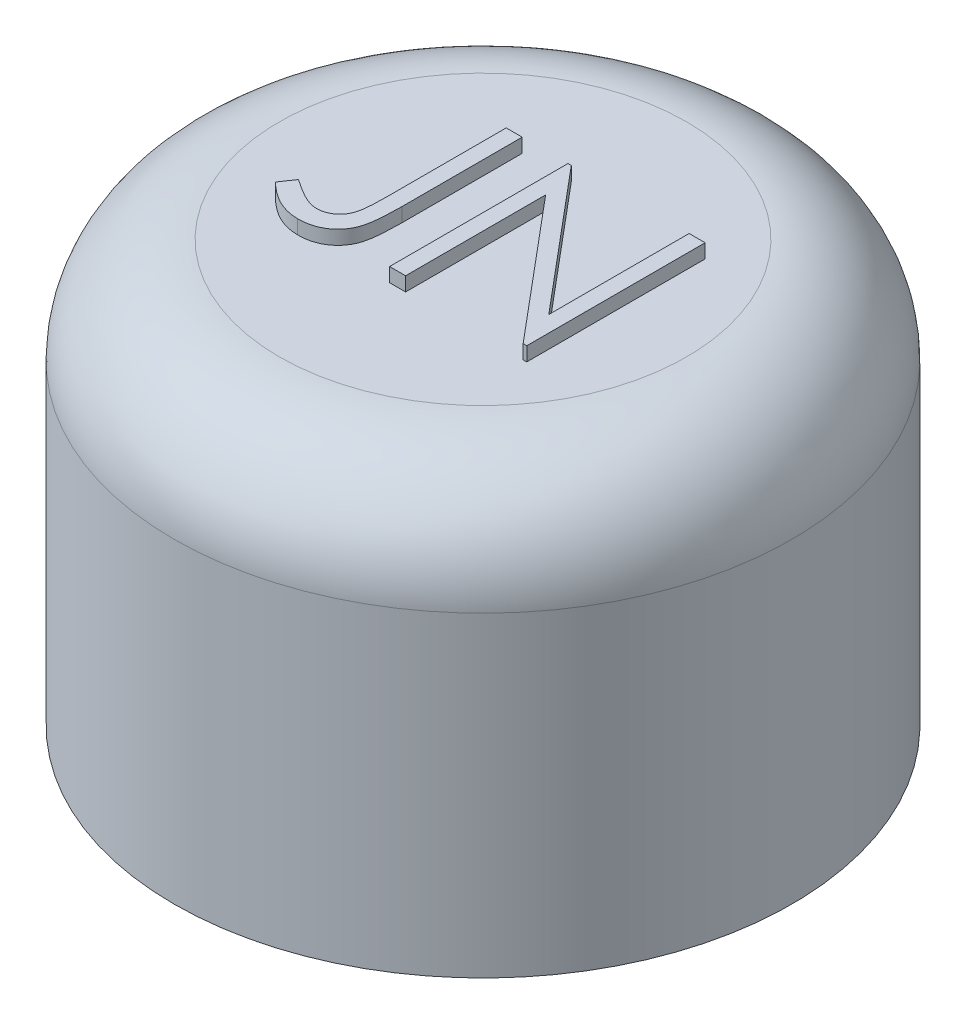
SolidWorks part; units mm, degrees
ref_plane "Front Plane" through (0, 0, 0) normal (0, 0, 1) x (1, 0, 0)
ref_plane "Top Plane" through (0, 0, 0) normal (0, 1, 0) x (1, 0, 0)
ref_plane "Right Plane" through (0, 0, 0) normal (1, 0, 0) x (0, 0, -1)
sketch "Sketch1" plane through (0, 0, 0) normal (0, 1, 0) x (1, 0, 0)
  circle A0 centre (0, 13) radius 4.5
  circle A2 centre (-11.2583, 6.5) radius 4.5
  circle A3 centre (-11.2583, -6.5) radius 4.5
  circle A4 centre (11.2583, 6.5) radius 4.5
  circle A5 centre (11.2583, -6.5) radius 4.5
  circle A6 centre (0, -13) radius 4.5
  dimension "D1" = 13
sketch "Sketch2" plane through (0, 30, 0) normal (0, 1, 0) x (1, 0, 0)
  circle A6 centre (0, 0) radius 22
extrude "Boss-Extrude3" add sketch "Sketch2" against normal blind 30
extrude "Cut-Extrude2" cut sketch "Sketch1" along normal blind 25
fillet "Fillet1" radius 7.5 1 edges at (0, 30, 22)
sketch "Sketch3" plane through (0, 30, 0) normal (0, 1, 0) x (1, 0, 0)
  text T0 "JN" font "Century Gothic" height in points 48
extrude "Boss-Extrude4" add sketch "Sketch3" along normal blind 1
